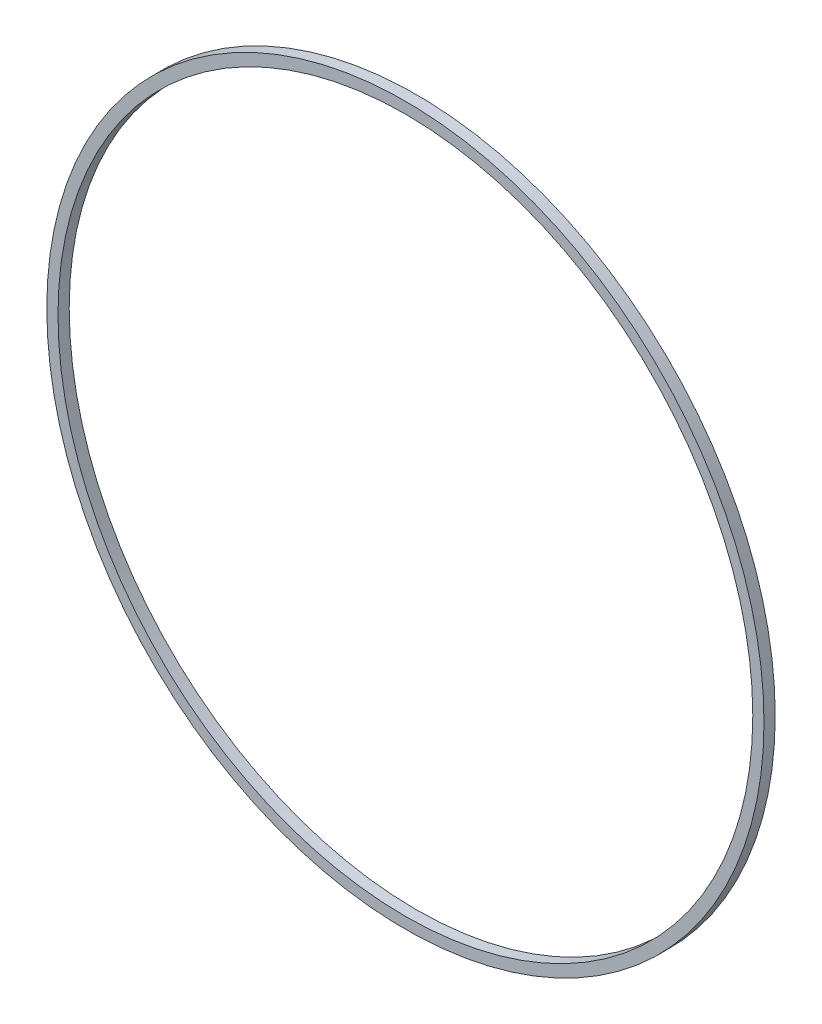
SolidWorks part; units mm, degrees
ref_plane "Piano frontale" through (0, 0, 0) normal (0, 0, 1) x (1, 0, 0)
ref_plane "Piano superiore" through (0, 0, 0) normal (0, 1, 0) x (1, 0, 0)
ref_plane "Piano destro" through (0, 0, 0) normal (1, 0, 0) x (0, 0, -1)
sketch "Schizzo1" plane through (0, 0, 0) normal (0, 0, 1) x (1, 0, 0)
  circle A0 centre (0, 0) radius 16
  circle A1 centre (0, 0) radius 15.5
  dimension "D1" = 32
  dimension "D2" = 31
extrude "Estrusione-Estrusione1" add sketch "Schizzo1" along normal blind 0.5
